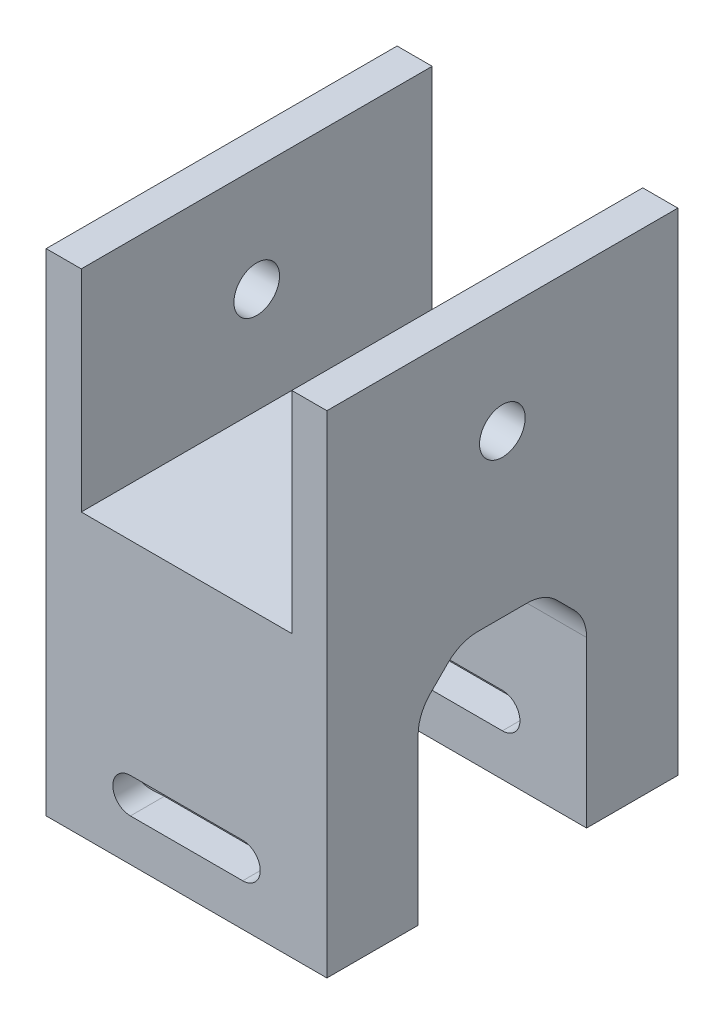
SolidWorks part; units mm, degrees
material "ABS PC"
ref_plane "Front Plane" through (0, 0, 0) normal (0, 0, 1) x (1, 0, 0)
ref_plane "Top Plane" through (0, 0, 0) normal (0, 1, 0) x (1, 0, 0)
ref_plane "Right Plane" through (0, 0, 0) normal (1, 0, 0) x (0, 0, -1)
sketch "Sketch1" plane through (0, 0, 0) normal (0, 1, 0) x (1, 0, 0)
  line L1 (0, 0) -> (40, 0)
  line L2 (0, 0) -> (0, 50)
  line L3 (0, 50) -> (40, 50)
  line L4 (40, 0) -> (40, 50)
  dimension "D1" = 50
  dimension "D2" = 40
extrude "Boss-Extrude1" add sketch "Sketch1" along normal blind 70
sketch "Sketch2" plane through (0, 0, 0) normal (0, 0, 1) x (1, 0, 0)
  line L0 (0, 70) -> (40, 70) construction
  line L1 (5, 70) -> (35, 70)
  line L2 (5, 70) -> (5, 40)
  line L3 (5, 40) -> (35, 40)
  line L4 (35, 70) -> (35, 40)
  line L5 (0, 70) -> (0, 0) construction
  dimension "D1" = 30
  dimension "D2" = 30
  dimension "D3" = 5
extrude "Cut-Extrude1" cut sketch "Sketch2" against normal through all
sketch "Sketch3" plane through (0, 0, 0) normal (-1, 0, 0) x (0, 0, 1)
  line L0 (-37, 0) -> (-13, 0)
  line L1 (-37, 0) -> (-37, 32)
  line L2 (-13, 0) -> (-13, 32)
  line L3 (-37, 32) -> (-13, 32)
  line L4 (-50, 0) -> (0, 0) construction
  line L5 (-50, 70) -> (-50, 0) construction
  line L6 (0, 70) -> (0, 0) construction
  line L7 (-37, 16) -> (-13, 16) construction
  dimension "D1" = 13
  dimension "D2" = 13
  dimension "D3" = 8
extrude "Cut-Extrude2" cut sketch "Sketch3" against normal through all
sketch "Sketch5" plane through (0, 0, 0) normal (-1, 0, 0) x (0, 0, 1)
  line L0 (-37, 32) -> (-37, 0) construction
  line L1 (-13, 0) -> (0, 0) construction
  line L2 (-13, 0) -> (-13, 32) construction
  circle A0 centre (-43.5, 8.5) radius 3
  circle A1 centre (-6.5, 8.5) radius 3
  dimension "D1" = 6
  dimension "D2" = 6.5
  dimension "D3" = 6.5
  dimension "D4" = 8.5
sketch "Sketch8" plane through (0, 0, 0) normal (-1, 0, 0) x (0, 0, 1)
  line L0 (-50, 70) -> (0, 70) construction
  line L1 (-25, 70) -> (-25, 32) construction
  line L2 (-13, 32) -> (-37, 32) construction
  circle A0 centre (-25, 55) radius 3.25
  dimension "D1" = 6.5
  dimension "D2" = 15
extrude "Cut-Extrude6" cut sketch "Sketch8" against normal through all
extrude "Cut-Extrude7" cut sketch "Sketch5" against normal offset from surface (36 mm away) 4 up to face at (40, 55, -21.75)
sketch "Sketch9" plane through (0, 0, 0) normal (0, -1, 0) x (1, 0, 0)
  line L0 (4, -47.5) -> (4, -39.5)
  line L1 (4, -47.5) -> (8, -47.5)
  line L2 (4, -39.5) -> (8, -39.5)
  line L3 (8, -47.5) -> (8, -39.5)
  line L4 (4, -10.5) -> (4, -2.5)
  line L5 (4, -10.5) -> (8, -10.5)
  line L6 (4, -2.5) -> (8, -2.5)
  line L7 (8, -10.5) -> (8, -2.5)
  line L8 (0, -50) -> (0, -37) construction
  line L9 (40, -37) -> (0, -37) construction
  line L10 (40, -13) -> (0, -13) construction
  dimension "D1" = 8
  dimension "D2" = 4
  dimension "D3" = 4
  dimension "D4" = 2.5
  dimension "D5" = 2.5
extrude "Cut-Extrude8" cut sketch "Sketch9" against normal blind 18
sketch "Sketch10" plane through (0, 0, 0) normal (0, 0, 1) x (1, 0, 0)
  line L0 (28, 8.5) -> (12, 8.5) construction
  line L1 (28, 6) -> (12, 6)
  line L2 (28, 11) -> (12, 11)
  line L3 (40, 70) -> (40, 0) construction
  line L4 (0, 0) -> (40, 0) construction
  arc A0 (28, 6) -> (28, 11) centre (28, 8.5) ccw
  arc A1 (12, 11) -> (12, 6) centre (12, 8.5) ccw
  point P2 (20, 8.5)
  dimension "D1" = 5
  dimension "D2" = 4
  dimension "D3" = 12
  dimension "D4" = 8.5
extrude "Cut-Extrude9" cut sketch "Sketch10" against normal through all
chamfer "Chamfer2" distance 10 angle 65 1 edges at (0, 32, -25)
fillet "Fillet3" radius 40 1 edges at (21.4451, 32, -25)
chamfer "Chamfer4" distance 6 angle 45 6 edges at (6.7041, 38.8738, -13) (21.6553, 32.9482, -13) (35.1564, 32, -13) (6.7041, 38.8738, -37) (21.6553, 32.9482, -37) (35.1564, 32, -37)
fillet "Fillet4" radius 6 12 edges at (35.1564, 26, -13) (20.3566, 27.0904, -13) (35.1564, 26, -37) (20.3566, 27.0904, -37) (35.1564, 32, -31) (21.6553, 32.9482, -31) (35.1564, 32, -19) (21.6553, 32.9482, -19) (5.4362, 32.8448, -13) (5.4362, 32.8448, -37) (6.7041, 38.8738, -31) (6.7041, 38.8738, -19)
